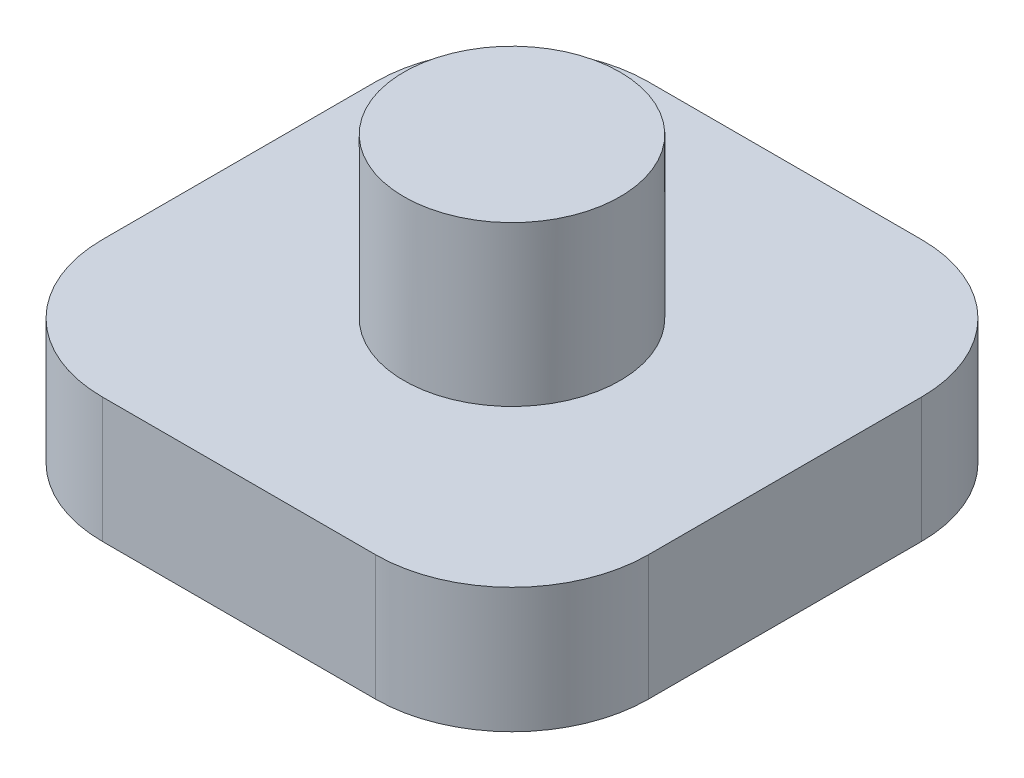
SolidWorks part; units mm, degrees
ref_plane "Front Plane" through (0, 0, 0) normal (0, 0, 1) x (1, 0, 0)
ref_plane "Top Plane" through (0, 0, 0) normal (0, 1, 0) x (1, 0, 0)
ref_plane "Right Plane" through (0, 0, 0) normal (1, 0, 0) x (0, 0, -1)
sketch "Sketch1" plane through (0, 0, 0) normal (0, 1, 0) x (1, 0, 0)
  line L1 (0, 0) -> (12, 0)
  line L2 (0, 0) -> (0, 12)
  line L3 (0, 12) -> (12, 12)
  line L4 (12, 0) -> (12, 12)
  dimension "D1" = 12
  dimension "D2" = 12
extrude "Boss-Extrude1" add sketch "Sketch1" along normal blind 2.75
sketch "Sketch3" plane through (0, 2.75, 0) normal (0, 1, 0) x (1, 0, 0)
  line L0 (0, 12) -> (0, 0) construction
  line L1 (0, 0) -> (12, 0) construction
  circle A0 centre (6, 6) radius 2.375
  dimension "D3" = 4.75
  dimension "D1" = 6
  dimension "D2" = 6
extrude "Boss-Extrude2" add sketch "Sketch3" along normal blind 3.5
fillet "Fillet1" radius 3 4 edges at (12, 1.375, -12) (12, 1.375, 0) (0, 1.375, -12) (0, 1.375, 0)
